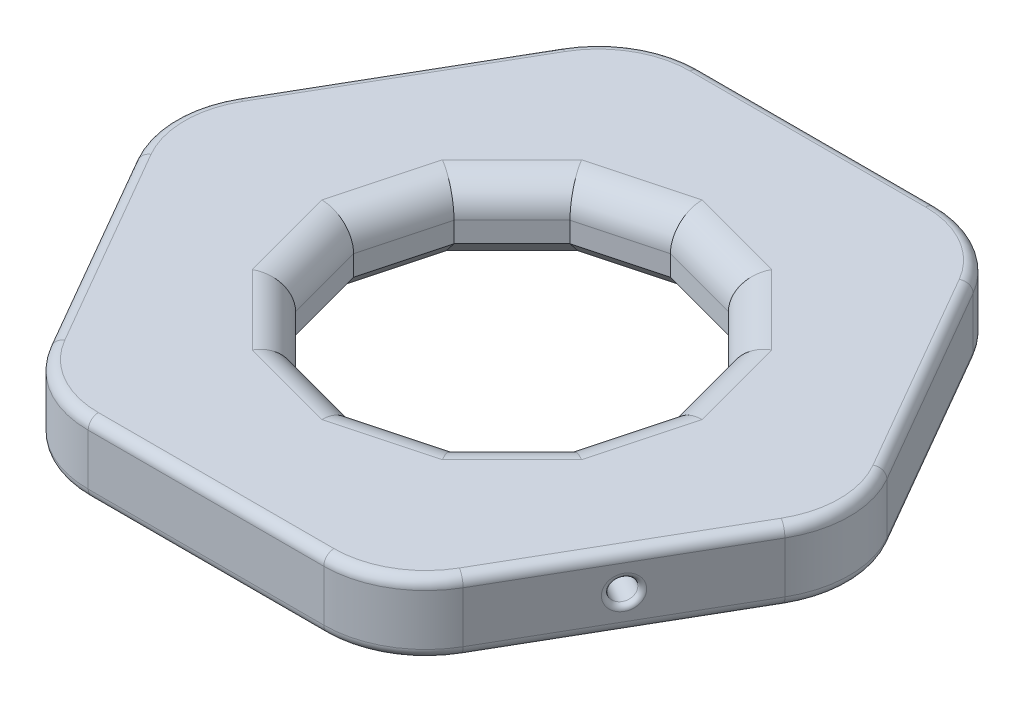
SolidWorks part; units mm, degrees
ref_plane "Alzado" through (0, 0, 0) normal (0, 0, 1) x (1, 0, 0)
ref_plane "Planta" through (0, 0, 0) normal (0, 1, 0) x (1, 0, 0)
ref_plane "Vista lateral" through (0, 0, 0) normal (1, 0, 0) x (0, 0, -1)
sketch "Croquis1" plane through (0, 0, 0) normal (0, 1, 0) x (1, 0, 0)
  line L1 (34.641, 0) -> (17.3205, 30)
  line L2 (17.3205, 30) -> (-17.3205, 30)
  line L3 (-17.3205, 30) -> (-34.641, 0)
  line L4 (-34.641, 0) -> (-17.3205, -30)
  line L5 (-17.3205, -30) -> (17.3205, -30)
  line L6 (17.3205, -30) -> (34.641, 0)
  circle A0 centre (0, 0) radius 30 construction
extrude "Saliente-Extruir1" add sketch "Croquis1" along normal blind 7
sketch "Croquis2" plane through (25.9808, 0, 15) normal (0.866, 0, 0.5) x (0.5, 0, -0.866)
  line L0 (-17.3205, 7) -> (17.3205, 0) construction
  circle A0 centre (0, 3.5) radius 1.125
  dimension "D1" = 2.25
extrude "Cortar-Extruir1" cut sketch "Croquis2" against normal blind 10
sketch "Croquis3" plane through (0, 7, 0) normal (0, 1, 0) x (1, 0, 0)
  circle A0 centre (0, 0) radius 12.3301
sketch "Croquis4" plane through (-25.9808, 0, 15) normal (-0.866, 0, 0.5) x (0.5, 0, 0.866)
  line L0 (-17.3205, 7) -> (17.3205, 0) construction
  circle A0 centre (0, 3.5) radius 1.125
  dimension "D1" = 2.25
extrude "Cortar-Extruir2" cut sketch "Croquis4" against normal blind 10
sketch "Croquis5" plane through (0, 0, -30) normal (0, 0, -1) x (-1, 0, 0)
  line L0 (-17.3205, 7) -> (17.3205, 0) construction
  circle A0 centre (0, 3.5) radius 1.125
  dimension "D1" = 2.25
extrude "Cortar-Extruir3" cut sketch "Croquis5" against normal blind 10
fillet "Redondeo1" radius 10 6 edges at (17.3205, 3.5, 30) (34.641, 3.5, 0) (17.3205, 3.5, -30) (-17.3205, 3.5, 30) (-34.641, 3.5, 0) (-17.3205, 3.5, -30)
fillet "Redondeo2" radius 0.5 3 edges at (26.5433, 3.5, 14.0257) (-25.4183, 3.5, 15.9743) (-1.125, 3.5, -30)
fillet "Redondeo3" radius 1 12 edges at (-16.547, 7, -28.6603) (0, 7, -30) (16.547, 7, -28.6603) (25.9808, 7, -15) (33.094, 7, 0) (25.9808, 7, 15) (16.547, 7, 28.6603) (0, 7, 30) (-16.547, 7, 28.6603) (-25.9808, 7, 15) (-33.094, 7, 0) (-25.9808, 7, -15)
sketch "Croquis6" plane through (0, 7, 0) normal (0, 1, 0) x (1, 0, 0)
  line L1 (-15.5291, 0) -> (-13.4486, -7.7646)
  line L2 (-13.4486, -7.7646) -> (-7.7646, -13.4486)
  line L3 (-7.7646, -13.4486) -> (0, -15.5291)
  line L4 (0, -15.5291) -> (7.7646, -13.4486)
  line L5 (7.7646, -13.4486) -> (13.4486, -7.7646)
  line L6 (13.4486, -7.7646) -> (15.5291, 0)
  line L7 (15.5291, 0) -> (13.4486, 7.7646)
  line L8 (13.4486, 7.7646) -> (7.7646, 13.4486)
  line L9 (7.7646, 13.4486) -> (0, 15.5291)
  line L10 (0, 15.5291) -> (-7.7646, 13.4486)
  line L11 (-7.7646, 13.4486) -> (-13.4486, 7.7646)
  line L12 (-13.4486, 7.7646) -> (-15.5291, 0)
  circle A0 centre (0, 0) radius 15 construction
extrude "Cortar-Extruir4" cut sketch "Croquis6" against normal blind 10
fillet "Redondeo4" radius 3 12 edges at (14.4889, 7, -3.8823) (14.4889, 7, 3.8823) (10.6066, 7, 10.6066) (3.8823, 7, 14.4889) (-3.8823, 7, 14.4889) (-10.6066, 7, 10.6066) (-14.4889, 7, 3.8823) (-14.4889, 7, -3.8823) (-10.6066, 7, -10.6066) (-3.8823, 7, -14.4889) (3.8823, 7, -14.4889) (10.6066, 7, -10.6066)
fillet "Redondeo5" radius 1 12 edges at (33.094, 0, 0) (25.9808, 0, 15) (16.547, 0, 28.6603) (0, 0, 30) (-16.547, 0, 28.6603) (-25.9808, 0, 15) (-33.094, 0, 0) (-25.9808, 0, -15) (-16.547, 0, -28.6603) (0, 0, -30) (16.547, 0, -28.6603) (25.9808, 0, -15)
chamfer "Chaflán1" distance 2 angle 45 12 edges at (-3.8823, 0, 14.4889) (-10.6066, 0, 10.6066) (-14.4889, 0, 3.8823) (-14.4889, 0, -3.8823) (-10.6066, 0, -10.6066) (-3.8823, 0, -14.4889) (3.8823, 0, -14.4889) (10.6066, 0, -10.6066) (14.4889, 0, -3.8823) (14.4889, 0, 3.8823) (10.6066, 0, 10.6066) (3.8823, 0, 14.4889)
